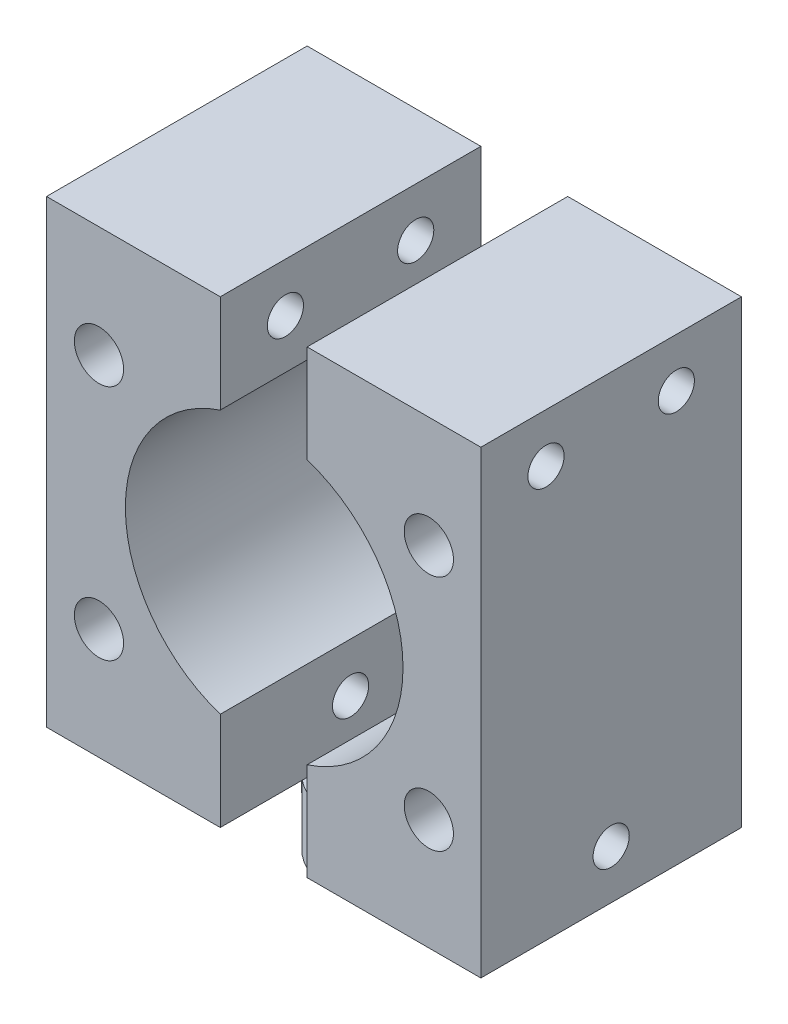
SolidWorks part; units mm, degrees
material "Plain Carbon Steel"
ref_plane "Front Plane" through (0, 0, 0) normal (0, 0, 1) x (1, 0, 0)
ref_plane "Top Plane" through (0, 0, 0) normal (0, 1, 0) x (1, 0, 0)
ref_plane "Right Plane" through (0, 0, 0) normal (1, 0, 0) x (0, 0, -1)
sketch "Sketch1" plane through (0, 0, 0) normal (0, 1, 0) x (1, 0, 0)
  line L0 (0, 4.75) -> (0, -4.75) construction
  line L1 (1.5, 4.5069) -> (1.5, -4.5069)
  line L2 (-1.5, 4.5069) -> (-1.5, -4.5069)
  circle A0 centre (0, 0) radius 4.75
  dimension "D1" = 9.5
  dimension "D2" = 1.5
ref_plane "GroundPlane" through (0, 4.5, 0) normal (0, 1, 0) x (-1, 0, 0)
sketch "Sketch2" plane through (0, 4.5, 0) normal (0, 1, 0) x (-1, 0, 0)
  line L0 (0, 7.5) -> (6.4952, -3.75) construction
  line L1 (0, 7.5) -> (0, -7.5) construction
  line L2 (0, 12.7) -> (0, -12.7) construction
  line L3 (0, 7.5) -> (-6.4952, -3.75) construction
  line L4 (-9.2393, -11.2686) -> (9.8107, -11.2686) construction
  line L5 (-9.2393, -11.2686) -> (-9.2393, -30.3186) construction
  line L6 (-9.2393, -30.3186) -> (9.8107, -30.3186) construction
  line L7 (9.8107, -11.2686) -> (9.8107, -30.3186) construction
  line L8 (-6.4952, -3.75) -> (6.4952, -3.75) construction
  line L9 (0, -7.5) -> (6.4952, 3.75) construction
  line L10 (6.4952, 3.75) -> (-6.4952, 3.75) construction
  line L11 (-6.4952, 3.75) -> (0, -7.5) construction
  line L12 (3, -8.6561) -> (3, 9.3439)
  line L13 (3, -8.6561) -> (15, -8.6561)
  line L14 (3, 9.3439) -> (15, 9.3439)
  line L15 (15, 9.3439) -> (15, -8.6561)
  line L16 (-3, -8.6561) -> (-3, 9.3439)
  line L17 (-3, -8.6561) -> (-15, -8.6561)
  line L18 (-3, 9.3439) -> (-15, 9.3439)
  line L19 (-15, 9.3439) -> (-15, -8.6561)
  circle A0 centre (0, 0) radius 7.5 construction
  dimension "D1" = 15
  dimension "D2" = 30
  dimension "D3" = 25.4
  dimension "D4" = 19.05
  dimension "D5" = 19.05
  dimension "D6" = 30
  dimension "D7" = 30
  dimension "D8" = 3
  dimension "D9" = 18
  dimension "D10" = 12
ref_plane "TopPlane" through (0, 36.25, 0) normal (0, 1, 0) x (-1, 0, 0)
extrude "Extrude1" add sketch "Sketch2" along normal blind 31.75
extrude "Extrude2" add sketch "Sketch1" along normal blind 4.5 contours L1 A0 | L2 A0
sketch "Sketch4" plane through (0, 0, 9.3439) normal (0, 0, 1) x (1, 0, 0)
  line L0 (-14.9586, 36.25) -> (15.0262, 4.5) construction
  line L1 (9.9, 36.25) -> (-9.9, 36.25) construction
  line L2 (9.9, 4.5) -> (-9.9, 4.5) construction
  line L3 (15.0262, 36.25) -> (-14.9586, 4.5) construction
  circle A0 centre (0.0338, 20.375) radius 9.5885
  point P8 (0.0338, 20.375)
  dimension "D1" = 19.177
extrude "Extrude3" cut sketch "Sketch4" against normal blind 17
sketch "Sketch6" plane through (15, 0, 0) normal (1, 0, 0) x (0, 0, -1)
  line L0 (-9.3439, 36.25) -> (-9.3439, 4.5) construction
  line L1 (-9.3439, 20.375) -> (8.6561, 20.375) construction
  line L2 (8.6561, 36.25) -> (8.6561, 4.5) construction
  line L3 (-0.3439, 36.25) -> (-0.3439, 4.5) construction
  line L4 (-9.3439, 36.25) -> (8.6561, 36.25) construction
  line L5 (-9.3439, 4.5) -> (8.6561, 4.5) construction
  line L6 (-0.3439, 36.25) -> (-9.3439, 29.4932) construction
  point P12 (-4.8439, 32.8716)
  point P15 (4.1561, 32.8716)
  point P16 (4.1561, 7.8784)
  point P17 (-4.8439, 7.8784)
  point P18 (-0.3439, 32.8716)
  point P19 (-0.3439, 7.8784)
sketch "Sketch9" plane through (0, 0, 9.3439) normal (0, 0, 1) x (1, 0, 0)
  line L0 (-15, 31.1716) -> (-7.7544, 25.9681) construction
  line L1 (-15, 9.5784) -> (-7.7544, 14.7819) construction
  line L2 (15, 9.5784) -> (7.81, 14.7652) construction
  line L3 (15, 36.25) -> (15, 4.5) construction
  line L4 (15, 31.1716) -> (7.81, 25.9848) construction
  line L5 (15, 36.25) -> (15, 29.4932) construction
  line L6 (-15, 31.1716) -> (15, 31.1716) construction
  line L7 (16.5, 36.25) -> (-16.5, 36.25) construction
  arc A0 (-3, 29.4709) -> (-3, 11.2791) centre (0.0338, 20.375) ccw construction
  arc A1 (3, 11.2568) -> (3, 29.4932) centre (0.0338, 20.375) ccw construction
  point P20 (-11.3772, 28.5699)
  point P21 (-11.3772, 12.1801)
  point P22 (11.405, 12.1718)
  point P23 (11.405, 28.5782)
  dimension "D1" = 5.0784
hole_wizard "M3 Clearance Hole1" positions "3DSketch2" profile "Sketch11" hole size "M3" standard "Ansi Metric" end condition through all
sketch3d "3DSketch2"
  point P0 (-11.3772, 28.5699, 9.3439)
  point P3 (-11.3772, 12.1801, 9.3439)
  point P6 (11.405, 12.1718, 9.3439)
  point P9 (11.405, 28.5782, 9.3439)
sketch "Sketch11" plane through (-11.3772, 28.5699, 9.3439) normal (1, 0, 0) x (0, -1, 0)
  line L0 (0, 0) -> (0, 18)
  line L1 (0, 18) -> (1.7, 18)
  line L2 (1.7, 18) -> (1.7, 0)
  line L5 (1.7, 0) -> (0, 0)
  line L11 (0, -6.35) -> (0, 107.95) construction
  dimension "Thru Hole Dia." = 3.4
  dimension "Thru Hole Depth" = 18
sketch "Sketch14" plane through (0, 4.5, 0) normal (0, 1, 0) x (-1, 0, 0)
  point P0 (6.4952, 3.75)
  point P1 (-6.4952, 3.75)
  point P3 (0, -7.5)
sketch "Sketch16" plane through (0, 4.5, 0) normal (0, 1, 0) x (-1, 0, 0)
  point P0 (6.4952, 3.75)
  point P1 (-6.4952, 3.75)
  point P3 (0, -7.5)
hole_wizard "M3x0.5 Tapped Hole1" positions "3DSketch3" profile "Sketch18" tap size "M3x0.5" standard "Ansi Metric" end condition through all
sketch3d "3DSketch3"
  point P0 (15, 32.8716, 4.8439)
  point P3 (15, 32.8716, -4.1561)
  point P6 (15, 7.8784, 0.3439)
sketch "Sketch18" plane through (15, 32.8716, 4.8439) normal (0, 1, 0) x (0, 0, -1)
  line L0 (0, 0) -> (0, 30)
  line L1 (0, 30) -> (1.25, 30)
  line L2 (1.25, 30) -> (1.25, 0)
  line L5 (1.25, 0) -> (0, 0)
  line L11 (0, -6.35) -> (0, 107.95) construction
  dimension "Thru Tap Drill Dia." = 2.5
  dimension "Thru Tap Drill Depth" = 30
cosmetic thread "Hole Thread6" parameters "D2"=3
cosmetic thread "Hole Thread7" parameters "D2"=3
cosmetic thread "Hole Thread8" parameters "D2"=3
